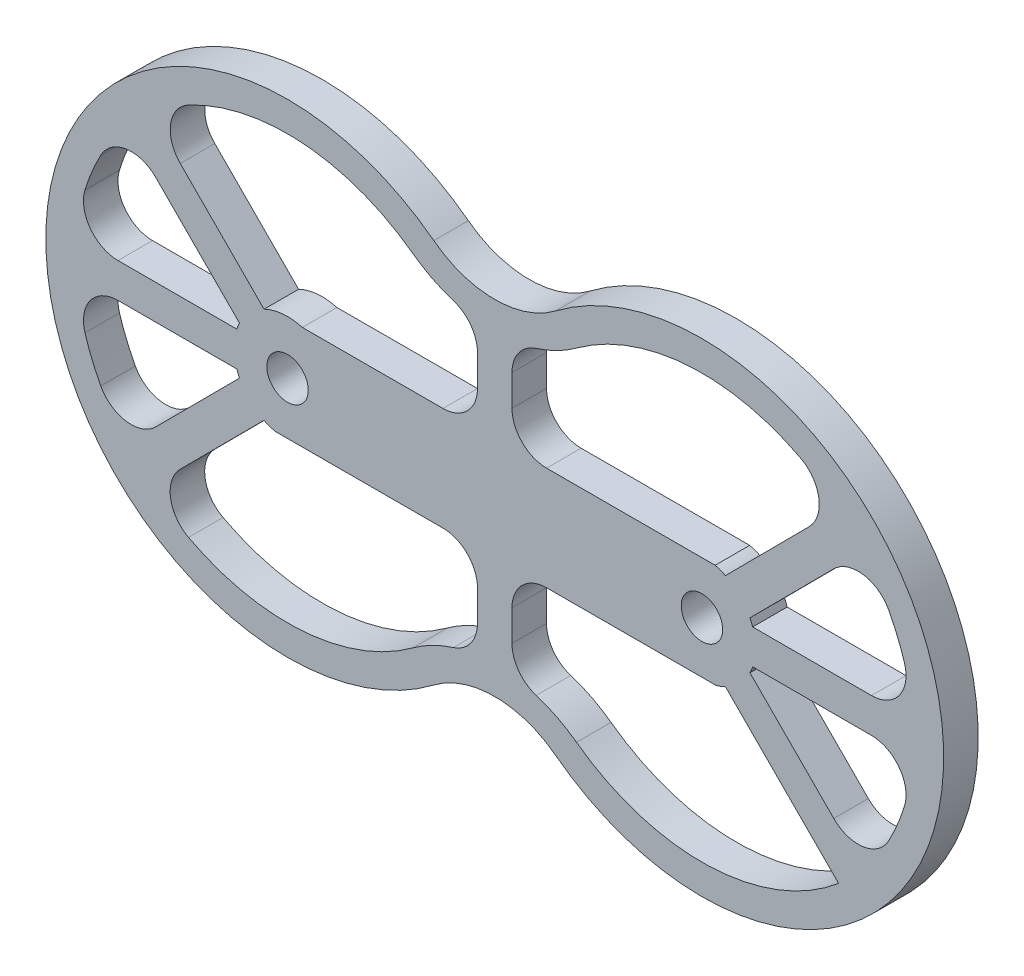
SolidWorks part; units mm, degrees
ref_plane "Front Plane" through (0, 0, 0) normal (0, 0, 1) x (1, 0, 0)
ref_plane "Top Plane" through (0, 0, 0) normal (0, 1, 0) x (1, 0, 0)
ref_plane "Right Plane" through (0, 0, 0) normal (1, 0, 0) x (0, 0, -1)
sketch "Sketch1" plane through (0, 0, 0) normal (0, 0, 1) x (1, 0, 0)
  line L0 (-176.5356, 0) -> (186.4453, 0) construction
  line L1 (-60.5278, 0) -> (59.4722, 0) construction
  line L2 (-56.236, 14.9127) -> (-5.5278, 14.9655)
  line L3 (-64.1239, -15.0956) -> (-5.5278, -15.0345)
  line L4 (-60.5278, 0) -> (-103.8237, 43.5603) construction
  line L5 (-60.5278, 0) -> (-64.7598, -4.2533) construction
  line L6 (-100.0782, 46.8847) -> (-67.3375, 13.944)
  line L7 (-107.1708, 39.8352) -> (-74.4301, 6.8945)
  line L8 (-121.6622, 5) -> (-75.2182, 5)
  line L9 (-121.6622, -5) -> (-75.2182, -5)
  line L10 (-107.1923, -39.81) -> (-74.4338, -6.887)
  line L11 (-100.1035, -46.8634) -> (-67.3451, -13.9403)
  line L12 (-0.5278, 103.5337) -> (-0.5278, 49.7834) construction
  line L13 (4.4722, 41.9807) -> (4.4722, 14.9759)
  line L14 (-5.5278, 41.9807) -> (-5.5278, 14.9655)
  line L15 (-0.5278, 42.0955) -> (-0.5278, -38.6618) construction
  line L16 (99.0479, -46.8634) -> (66.2894, -13.9403)
  line L17 (106.1366, -39.81) -> (73.3782, -6.887)
  line L18 (120.6065, -5) -> (74.1626, -5)
  line L19 (120.6065, 5) -> (74.1626, 5)
  line L20 (106.1151, 39.8352) -> (73.3745, 6.8945)
  line L21 (99.0226, 46.8847) -> (66.2819, 13.944)
  line L22 (4.4722, -15.0241) -> (63.5869, -14.9625)
  line L23 (4.4722, 14.9759) -> (63.3049, 15.0372)
  line L24 (-5.5278, -15.0345) -> (-5.5278, -41.9807)
  line L25 (4.4722, -15.0241) -> (4.4722, -41.9807)
  arc A0 (-24.2108, 49.4316) -> (-100.0782, 46.8847) centre (-60.5278, 0) ccw
  arc A1 (23.1552, -49.4316) -> (99.0479, -46.8634) centre (59.4722, 0) ccw
  arc A2 (-18.1652, 55.7262) -> (-18.1652, -55.7262) centre (-60.5278, 0) ccw
  arc A3 (17.1095, -55.7262) -> (17.1095, 55.7262) centre (59.4722, 0) ccw
  arc A4 (-18.1652, 55.7262) -> (17.1095, 55.7262) centre (-0.5278, 78.9272) ccw
  arc A5 (-18.1652, -55.7262) -> (17.1095, -55.7262) centre (-0.5278, -78.9272) cw
  arc A6 (23.1552, -49.4316) -> (4.4722, -41.9807) centre (-0.5278, -81.667) ccw
  arc A7 (23.1552, 49.4316) -> (4.4722, 41.9807) centre (-0.5278, 81.667) cw
  arc A8 (-56.236, 14.9127) -> (-67.3375, 13.944) centre (-60.5278, 0) ccw
  arc A9 (63.5869, -14.9625) -> (66.2894, -13.9403) centre (59.4722, 0) ccw
  circle A10 centre (-60.5278, 0) radius 6
  arc A11 (-5.5278, -41.9807) -> (-24.2108, -49.4316) centre (-0.5278, -81.667) ccw
  arc A12 (-5.5278, 41.9807) -> (-24.2108, 49.4316) centre (-0.5278, 81.667) cw
  circle A13 centre (59.4722, 0) radius 6
  arc A14 (-100.1035, -46.8634) -> (-24.2108, -49.4316) centre (-60.5278, 0) ccw
  arc A15 (-67.3451, -13.9403) -> (-64.1239, -15.0956) centre (-60.5278, 0) ccw
  arc A16 (-121.6622, -5) -> (-107.1923, -39.81) centre (-60.5278, 0) ccw
  arc A17 (-74.4301, 6.8945) -> (-75.2182, 5) centre (-60.5278, 0) ccw
  arc A18 (-107.1708, 39.8352) -> (-121.6622, 5) centre (-60.5278, 0) ccw
  arc A19 (99.0226, 46.8847) -> (23.1552, 49.4316) centre (59.4722, 0) ccw
  arc A20 (106.1366, -39.81) -> (120.6065, -5) centre (59.4722, 0) ccw
  arc A21 (73.3782, -6.887) -> (74.1626, -5) centre (59.4722, 0) ccw
  arc A22 (74.1626, 5) -> (73.3745, 6.8945) centre (59.4722, 0) ccw
  arc A23 (66.2819, 13.944) -> (63.3049, 15.0372) centre (59.4722, 0) ccw
  arc A24 (120.6065, 5) -> (106.1151, 39.8352) centre (59.4722, 0) ccw
  arc A25 (-75.2182, -5) -> (-74.4338, -6.887) centre (-60.5278, 0) ccw
  point P10 (-60.5278, 61.3385)
  point P11 (59.4722, 61.3385)
  point P12 (-60.5278, -61.3385)
  point P13 (59.4722, -61.3385)
  point P22 (-0.6392, 0)
  dimension "D1" = 120
  dimension "D2" = 30
  dimension "D3" = 10
  dimension "D4" = 10
  dimension "D9" = 12
  dimension "D5" = 10
  dimension "D6" = 5
  dimension "D7" = 5
  dimension "D8" = 5
  dimension "D10" = 10
  dimension "D11" = 5
extrude "Boss-Extrude2" add sketch "Sketch1" along normal blind 10 contours A15 L11 A14 A11 L24 L3 | A25 L9 A16 L10 | L7 A18 L8 A17 | L14 A12 A0 L6 A8 L2 | A23 L21 A19 A7 L13 L23 | A9 L22 L25 A6 A1 L16 | A21 L17 A20 L18 | L19 A24 L20 A22 | A13 | A10 | A2 A5 A3 A4
fillet "Fillet2" radius 10 19 edges at (-5.5278, 41.9807, 5) (4.4722, 41.9807, 5) (99.0226, 46.8847, 5) (4.4722, 14.9759, 5) (-5.5278, -15.0345, 5) (106.1151, 39.8352, 5) (120.6065, 5, 5) (120.6065, -5, 5) (106.1366, -39.81, 5) (4.4722, -15.0241, 5) (4.4722, -41.9807, 5) (-5.5278, -41.9807, 5) (-100.1035, -46.8634, 5) (-107.1923, -39.81, 5) (-121.6622, -5, 5) (-5.5278, 14.9655, 5) (-107.1708, 39.8352, 5) (-121.6622, 5, 5) (-100.0782, 46.8847, 5)
